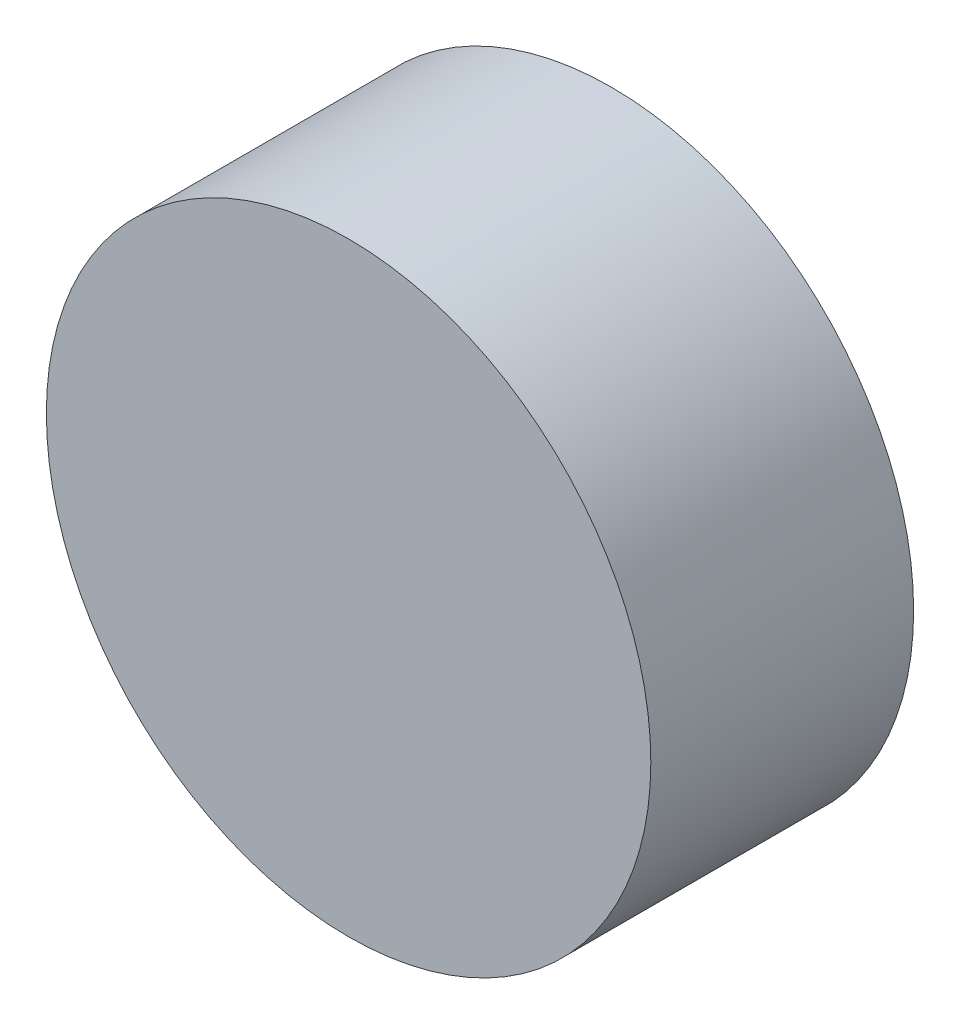
SolidWorks part; units mm, degrees
ref_plane "前基準面" through (0, 0, 0) normal (0, 0, 1) x (1, 0, 0)
ref_plane "上基準面" through (0, 0, 0) normal (0, 1, 0) x (1, 0, 0)
ref_plane "右基準面" through (0, 0, 0) normal (1, 0, 0) x (0, 0, -1)
sketch "草圖1" plane through (0, 0, 0) normal (0, 0, 1) x (1, 0, 0)
  circle A0 centre (0, 0) radius 5.75
  dimension "D1" = 11.5
extrude "填料-伸長1" add sketch "草圖1" along normal blind 5
